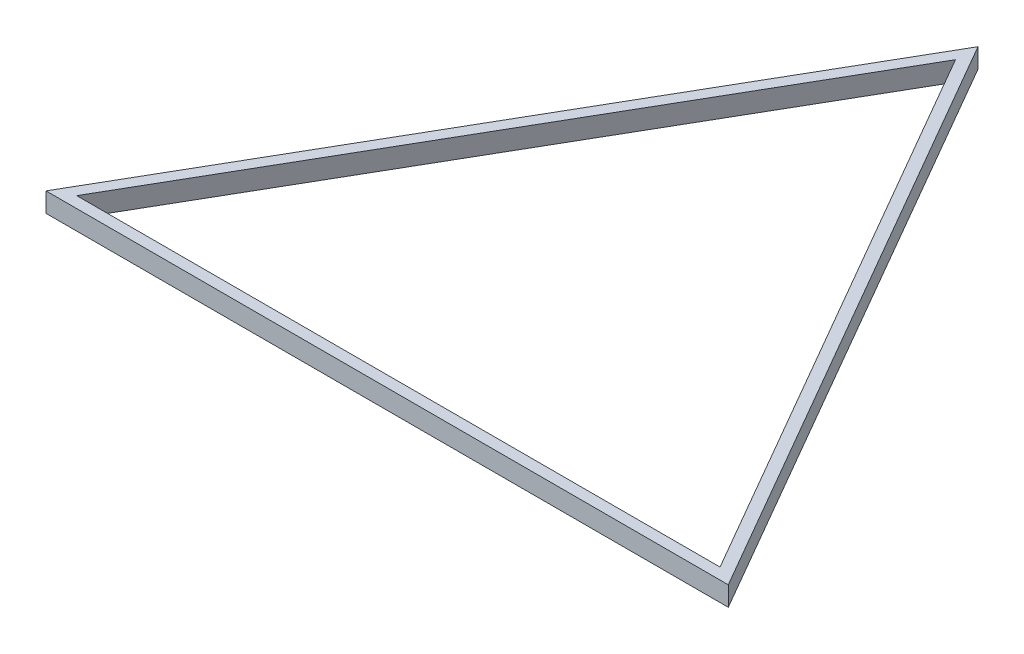
SolidWorks part; units mm, degrees
ref_plane "Front Plane" through (0, 0, 0) normal (0, 0, 1) x (1, 0, 0)
ref_plane "Top Plane" through (0, 0, 0) normal (0, 1, 0) x (1, 0, 0)
ref_plane "Right Plane" through (0, 0, 0) normal (1, 0, 0) x (0, 0, -1)
sketch "Sketch1" plane through (0, 0, 0) normal (0, 1, 0) x (1, 0, 0)
  line L1 (0, 404.1452) -> (-350, -202.0726)
  line L2 (-350, -202.0726) -> (350, -202.0726)
  line L3 (350, -202.0726) -> (0, 404.1452)
  line L4 (0, 381.0512) -> (-330, -190.5256)
  line L5 (-330, -190.5256) -> (330, -190.5256)
  line L6 (330, -190.5256) -> (0, 381.0512)
  circle A0 centre (0, 0) radius 202.0726 construction
  circle A1 centre (0, 0) radius 190.5256 construction
extrude "Boss-Extrude1" add sketch "Sketch1" along normal blind 20
